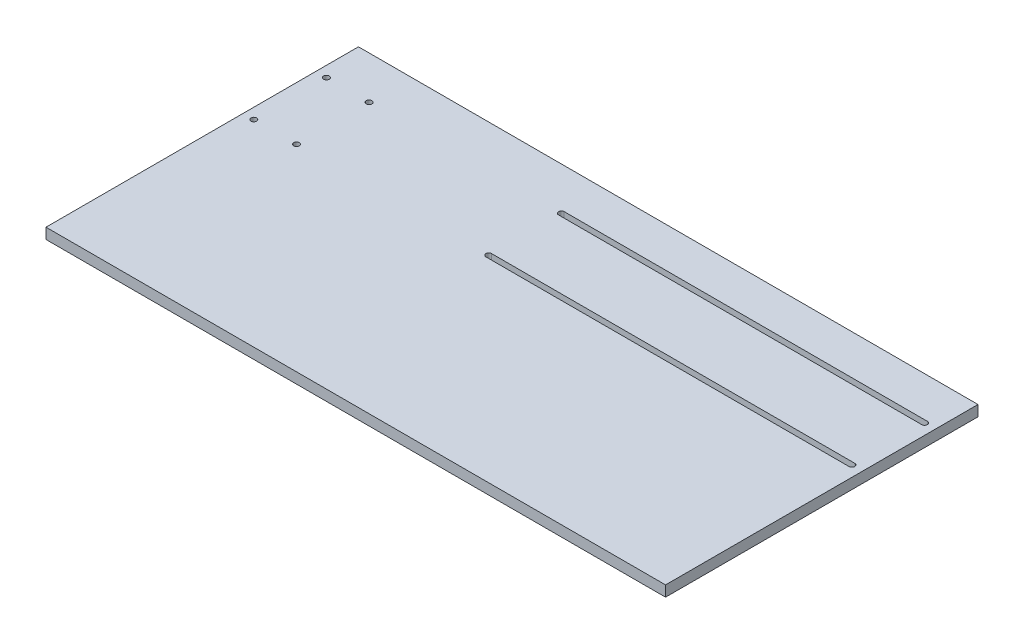
SolidWorks part; units mm, degrees
ref_plane "Front Plane" through (0, 0, 0) normal (0, 0, 1) x (1, 0, 0)
ref_plane "Top Plane" through (0, 0, 0) normal (0, 1, 0) x (1, 0, 0)
ref_plane "Right Plane" through (0, 0, 0) normal (1, 0, 0) x (0, 0, -1)
sketch "Sketch1" plane through (0, 0, 0) normal (0, 1, 0) x (1, 0, 0)
  line L1 (368.3, -185.7375) -> (-368.3, -185.7375)
  line L2 (368.3, -185.7375) -> (368.3, 185.7375)
  line L3 (368.3, 185.7375) -> (-368.3, 185.7375)
  line L4 (-368.3, -185.7375) -> (-368.3, 185.7375)
  line L5 (368.3, -185.7375) -> (-368.3, 185.7375) construction
  line L6 (368.3, 185.7375) -> (-368.3, -185.7375) construction
  point P0 (0, 0)
  dimension "D1" = 736.6
  dimension "D2" = 371.475
extrude "Boss-Extrude1" add sketch "Sketch1" along normal blind 12.7 contours L3 L4 L1 L2
sketch "Sketch2" plane through (0, 12.7, 0) normal (0, 1, 0) x (1, 0, 0)
  line L0 (-355.6, 134.9375) -> (-304.8, 48.5775) construction
  line L1 (-304.8, 134.9375) -> (-355.6, 48.5775) construction
  line L2 (368.3, 185.7375) -> (-368.3, 185.7375) construction
  line L3 (-368.3, -185.7375) -> (-368.3, 185.7375) construction
  line L4 (-76.2, 134.9375) -> (355.6, 134.9375) construction
  line L5 (-76.2, 138.3157) -> (355.6, 138.3157)
  line L6 (-76.2, 131.5593) -> (355.6, 131.5593)
  line L7 (-76.2, 48.5775) -> (355.6, 48.5775) construction
  line L8 (-76.2, 51.9557) -> (355.6, 51.9557)
  line L9 (-76.2, 45.1993) -> (355.6, 45.1993)
  line L10 (368.3, -185.7375) -> (368.3, 185.7375) construction
  circle A3 centre (-355.6, 134.9375) radius 3.3782
  circle A4 centre (-355.6, 48.5775) radius 3.3782
  circle A5 centre (-304.8, 48.5775) radius 3.3782
  circle A6 centre (-304.8, 134.9375) radius 3.3782
  arc A7 (-76.2, 138.3157) -> (-76.2, 131.5593) centre (-76.2, 134.9375) ccw
  arc A8 (355.6, 131.5593) -> (355.6, 138.3157) centre (355.6, 134.9375) ccw
  arc A9 (-76.2, 51.9557) -> (-76.2, 45.1993) centre (-76.2, 48.5775) ccw
  arc A10 (355.6, 45.1993) -> (355.6, 51.9557) centre (355.6, 48.5775) ccw
  point P10 (-330.2, 91.7575)
  point P11 (139.7, 134.9375)
  point P20 (139.7, 48.5775)
  dimension "D2" = 86.36
  dimension "D6" = 6.7564
  dimension "D7" = 3.3782
  dimension "D1" = 50.8
  dimension "D3" = 86.36
  dimension "D4" = 50.8
  dimension "D5" = 12.7
  dimension "D8" = 228.6
  dimension "D9" = 12.7
extrude "Cut-Extrude1" cut sketch "Sketch2" against normal through all
